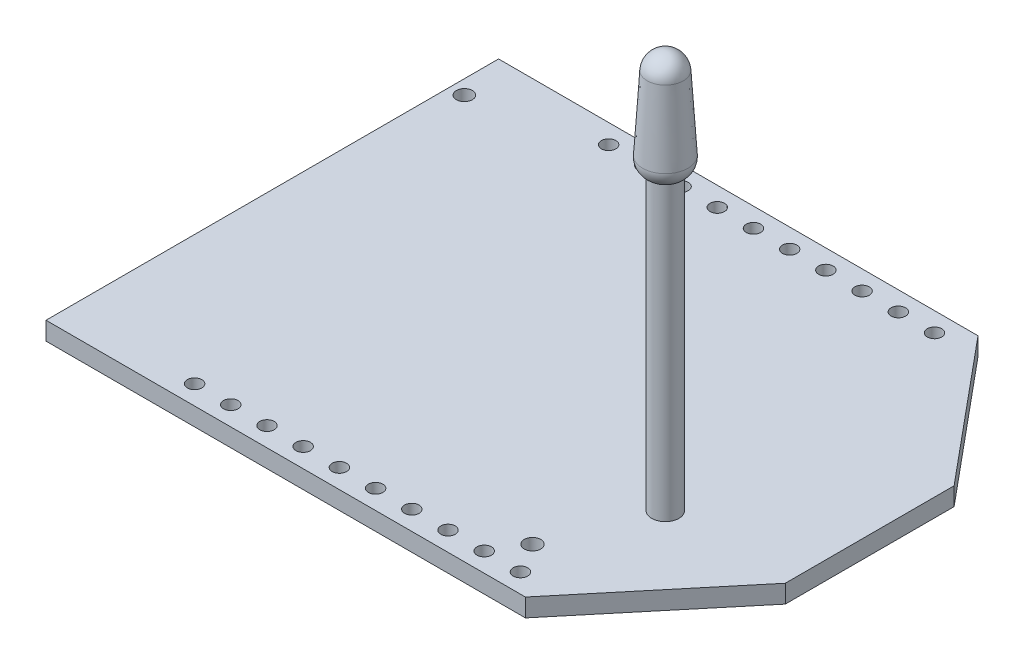
SolidWorks part; units mm, degrees
ref_plane "Front Plane" through (0, 0, 0) normal (0, 0, 1) x (1, 0, 0)
ref_plane "Top Plane" through (0, 0, 0) normal (0, 1, 0) x (1, 0, 0)
ref_plane "Right Plane" through (0, 0, 0) normal (1, 0, 0) x (0, 0, -1)
sketch "Sketch1" plane through (0, 0, 0) normal (0, 1, 0) x (1, 0, 0)
  line L1 (0, 0) -> (33, 0)
  line L2 (0, 0) -> (0, 25)
  line L3 (0, 25) -> (33, 25)
  line L4 (33, 0) -> (33, 25)
  dimension "D1" = 33
  dimension "D2" = 25
extrude "Boss-Extrude1" add sketch "Sketch1" along normal blind 1
sketch "Sketch2" plane through (0, 0, 0) normal (0, -1, 0) x (1, 0, 0)
  line L0 (33, -12.5) -> (0, -12.5) construction
  line L1 (33, 0) -> (33, -25) construction
  line L2 (0, -25) -> (0, 0) construction
  line L3 (33, 0) -> (26.483, 0)
  line L4 (0, 0) -> (33, 0) construction
  line L5 (26.483, 0) -> (33, -7.8378)
  line L6 (33, -7.8378) -> (33, 0)
  line L7 (33, -17.1622) -> (33, -25)
  line L8 (26.483, -25) -> (33, -17.1622)
  line L9 (33, -25) -> (26.483, -25)
extrude "Cut-Extrude1" cut sketch "Sketch2" against normal through all
sketch "Sketch3" plane through (0, 1, 0) normal (0, 1, 0) x (1, 0, 0)
  circle A0 centre (7.1439, 23.9361) radius 0.4
  circle A1 centre (9.1439, 23.9361) radius 0.4
  circle A2 centre (11.1439, 23.9361) radius 0.4
  circle A3 centre (13.1439, 23.9361) radius 0.4
  circle A4 centre (15.1439, 23.9361) radius 0.4
  circle A5 centre (17.1439, 23.9361) radius 0.4
  circle A6 centre (19.1439, 23.9361) radius 0.4
  circle A7 centre (21.1439, 23.9361) radius 0.4
  circle A8 centre (23.1439, 23.9361) radius 0.4
  circle A9 centre (25.1439, 23.9361) radius 0.4
  circle A10 centre (25.1439, 1.0639) radius 0.4
  circle A11 centre (23.1439, 1.0639) radius 0.4
  circle A12 centre (21.1439, 1.0639) radius 0.4
  circle A13 centre (19.1439, 1.0639) radius 0.4
  circle A14 centre (17.1439, 1.0639) radius 0.4
  circle A15 centre (15.1439, 1.0639) radius 0.4
  circle A16 centre (13.1439, 1.0639) radius 0.4
  circle A17 centre (11.1439, 1.0639) radius 0.4
  circle A18 centre (9.1439, 1.0639) radius 0.4
  circle A19 centre (7.1439, 1.0639) radius 0.4
  circle A20 centre (0.7843, 22.3251) radius 0.4421
  circle A22 centre (24.1527, 2.7223) radius 0.4582
  dimension "D1" = 0.8
  dimension "D2" = 10
extrude "Cut-Extrude2" cut sketch "Sketch3" against normal through all
sketch "Sketch4" plane through (0, 1, 0) normal (0, 1, 0) x (1, 0, 0)
  line L0 (0, 0) -> (26.483, 0) construction
  circle A0 centre (26.2119, 8) radius 0.75
  dimension "D1" = 1.5
  dimension "D2" = 8
extrude "Boss-Extrude2" add sketch "Sketch4" along normal blind 17
ref_plane "Plane1" through (0, 0, -8) normal (0, 0, 1) x (1, 0, 0)
sketch "Sketch5" plane through (0, 0, -8) normal (0, 0, 1) x (1, 0, 0)
  line L0 (26.2119, 18) -> (26.2119, 23)
  line L1 (26.9619, 18) -> (25.4619, 18) construction
  line L2 (25.2119, 22.0597) -> (24.9619, 18)
  line L3 (25.4619, 18) -> (25.4619, 1) construction
  line L4 (25.4619, 17.1284) -> (25.4619, 18)
  line L5 (25.4619, 18) -> (26.2119, 18)
  arc A0 (26.2119, 23) -> (25.2119, 22.0597) centre (26.2119, 21.9981) ccw
  arc A1 (24.9619, 18) -> (25.4619, 17.1284) centre (25.8737, 17.9438) ccw
  dimension "D1" = 1.25
  dimension "D2" = 1
  dimension "D3" = 0
  dimension "D4" = 5
revolve "Revolve1" add sketch "Sketch5" angle 360 about L0
sketch "Sketch6" plane through (0, 0, 0) normal (0, -1, 0) x (1, 0, 0)
  line L1 (24.5079, -22.429) -> (0.7782, -22.429)
  line L2 (25.0079, -21.929) -> (25.0079, -2.9033)
  line L3 (24.5079, -2.4033) -> (0.7782, -2.4033)
  line L4 (0.2782, -21.929) -> (0.2782, -2.9033)
  arc A0 (0.7782, -2.4033) -> (0.2782, -2.9033) centre (0.7782, -2.9033) ccw
  arc A1 (0.7782, -22.429) -> (0.2782, -21.929) centre (0.7782, -21.929) cw
  arc A2 (24.5079, -22.429) -> (25.0079, -21.929) centre (24.5079, -21.929) ccw
  arc A3 (25.0079, -2.9033) -> (24.5079, -2.4033) centre (24.5079, -2.9033) ccw
  dimension "D1" = 0.5
  dimension "D2" = 0.5
extrude "Boss-Extrude3" add sketch "Sketch6" along normal blind 2
